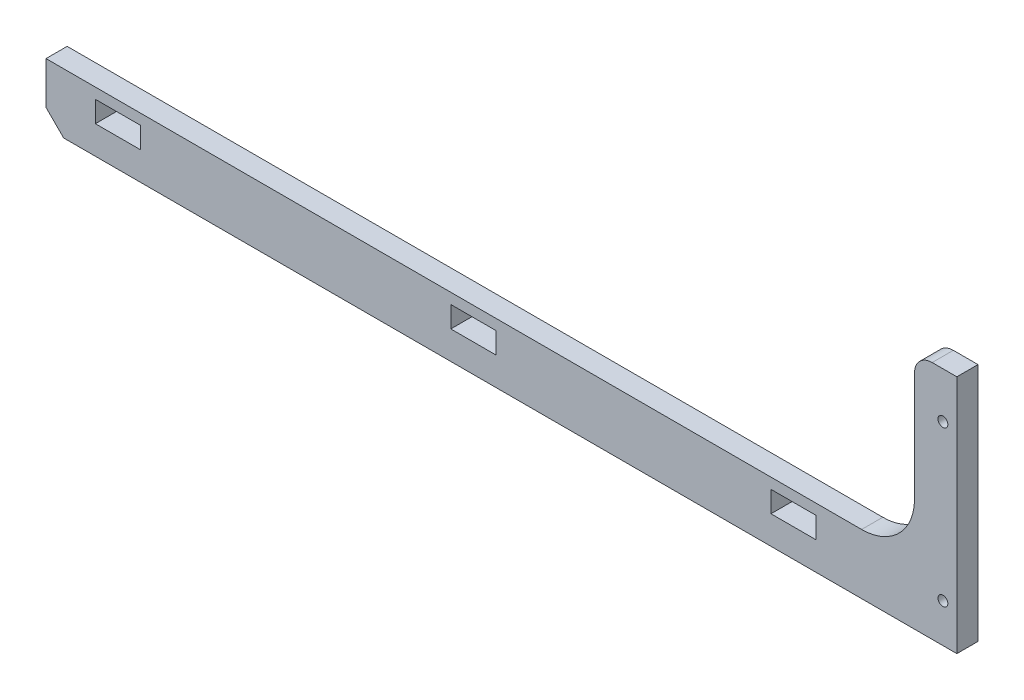
SolidWorks part; units mm, degrees
ref_plane "Front" through (0, 0, 0) normal (0, 0, 1) x (1, 0, 0)
ref_plane "Top" through (0, 0, 0) normal (0, 1, 0) x (1, 0, 0)
ref_plane "Right" through (0, 0, 0) normal (1, 0, 0) x (0, 0, -1)
sketch "Эскиз1" plane through (0, 0, 0) normal (0, 0, 1) x (1, 0, 0)
  line L0 (-165.3855, 0) -> (163.3727, 0) construction
  line L1 (-167.1826, 6) -> (64.1274, 6)
  line L2 (-167.1826, 6) -> (-167.1826, -6)
  line L4 (91.1274, 6) -> (91.1274, -11)
  line L5 (-162.1826, -11) -> (91.1274, -11)
  line L6 (-167.1826, -6) -> (-162.1826, -11)
  line L7 (51.2174, 3) -> (138.8459, 3) construction
  line L8 (91.1274, 6) -> (91.1274, 49)
  line L10 (51.2174, 42.1012) -> (51.2174, -60.2164) construction
  line L11 (-39.5826, 43.8022) -> (-39.5826, -70.5968) construction
  line L12 (38.4174, 3) -> (51.2174, 3)
  line L13 (38.4174, 3) -> (38.4174, -3)
  line L14 (38.4174, -3) -> (51.2174, -3)
  line L15 (51.2174, 3) -> (51.2174, -3)
  line L16 (38.4174, 3) -> (51.2174, -3) construction
  line L17 (38.4174, -3) -> (51.2174, 3) construction
  line L18 (-140.3826, 43.8022) -> (-140.3826, -35.6972) construction
  line L19 (-52.3826, 3) -> (-39.5826, 3)
  line L20 (-52.3826, 3) -> (-52.3826, -3)
  line L21 (-52.3826, -3) -> (-39.5826, -3)
  line L22 (-39.5826, 3) -> (-39.5826, -3)
  line L23 (-52.3826, 3) -> (-39.5826, -3) construction
  line L24 (-52.3826, -3) -> (-39.5826, 3) construction
  line L25 (79.1274, 44) -> (79.1274, 21)
  line L26 (-153.1826, 3) -> (-140.3826, 3)
  line L27 (-153.1826, 3) -> (-153.1826, -3)
  line L28 (-153.1826, -3) -> (-140.3826, -3)
  line L29 (-140.3826, 3) -> (-140.3826, -3)
  line L30 (-153.1826, 3) -> (-140.3826, -3) construction
  line L31 (-153.1826, -3) -> (-140.3826, 3) construction
  line L32 (87.1774, 0) -> (87.1774, 50.1588) construction
  line L33 (91.1274, 49) -> (91.1274, 57)
  line L34 (91.1274, 57) -> (84.1274, 57)
  line L35 (79.1274, 52) -> (79.1274, 44)
  arc A0 (79.1274, 21) -> (64.1274, 6) centre (64.1274, 21) cw
  circle A2 centre (87.1774, 0) radius 1.4
  circle A3 centre (87.1774, 44) radius 1.4
  arc A4 (84.1274, 57) -> (79.1274, 52) centre (84.1274, 52) ccw
  point P0 (0, 0)
  point P13 (44.8174, 0)
  point P20 (-45.9826, 0)
  point P27 (-146.7826, 0)
  point P38 (79.1274, 49)
  dimension "D15" = 15
  dimension "D16" = 5
  dimension "D17" = 2.8
  dimension "D18" = 3.95
  dimension "D19" = 2.8
  dimension "D2" = 39.91
  dimension "D3" = 12.8
  dimension "D4" = 6
  dimension "D5" = 90.8
  dimension "D6" = 12.8
  dimension "D7" = 6
  dimension "D8" = 100.8
  dimension "D9" = 6
  dimension "D10" = 12.8
  dimension "D11" = 3
  dimension "D12" = 46
  dimension "D13" = 17
  dimension "D14" = 12
  dimension "D20" = 8
extrude "Бобышка-Вытянуть1" add sketch "Эскиз1" along normal blind 6
